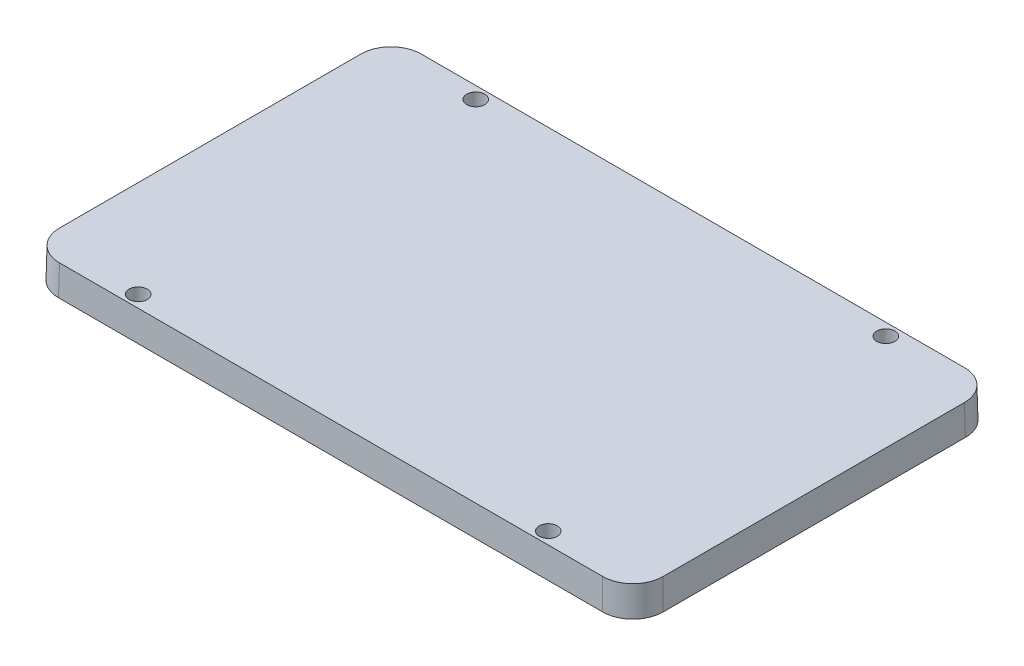
SolidWorks part; units mm, degrees
ref_plane "Front Plane" through (0, 0, 0) normal (0, 0, 1) x (1, 0, 0)
ref_plane "Top Plane" through (0, 0, 0) normal (0, 1, 0) x (1, 0, 0)
ref_plane "Right Plane" through (0, 0, 0) normal (1, 0, 0) x (0, 0, -1)
sketch "Sketch1" plane through (0, 0, 0) normal (0, 1, 0) x (1, 0, 0)
  line L1 (-50, 30) -> (50, 30)
  line L2 (-50, 30) -> (-50, -30)
  line L3 (-50, -30) -> (50, -30)
  line L4 (50, 30) -> (50, -30)
  line L5 (-50, 30) -> (50, -30) construction
  line L6 (-50, -30) -> (50, 30) construction
  point P0 (0, 0)
  dimension "D1" = 100
  dimension "D2" = 60
extrude "Boss-Extrude1" add sketch "Sketch1" along normal blind 5 draft 1
fillet "Fillet1" radius 5 4 edges at (49.9564, 2.5, 29.9564) (49.9564, 2.5, -29.9564) (-49.9564, 2.5, -29.9564) (-49.9564, 2.5, 29.9564)
sketch "Sketch2" plane through (0, 5, 0) normal (0, 1, 0) x (1, 0, 0)
  line L0 (-44.9135, -29.9127) -> (44.9135, -29.9127) construction
  line L1 (49.9127, -24.9135) -> (49.9127, 24.9135) construction
  circle A0 centre (33.9127, -27.9127) radius 1.5
  dimension "D1" = 3
  dimension "D2" = 2
  dimension "D3" = 16
extrude "Cut-Extrude1" cut sketch "Sketch2" against normal blind 5 draft 1 draft outward yes
mirror "Mirror1" about plane through (0, 0, 0) normal (0, 0, 1) of "Cut-Extrude1"
mirror "Mirror2" about plane through (0, 0, 0) normal (1, 0, 0) of "Mirror1", "Cut-Extrude1"
scale "Scale1" scale about centroid uniform scaling yes scale factor 1.05
